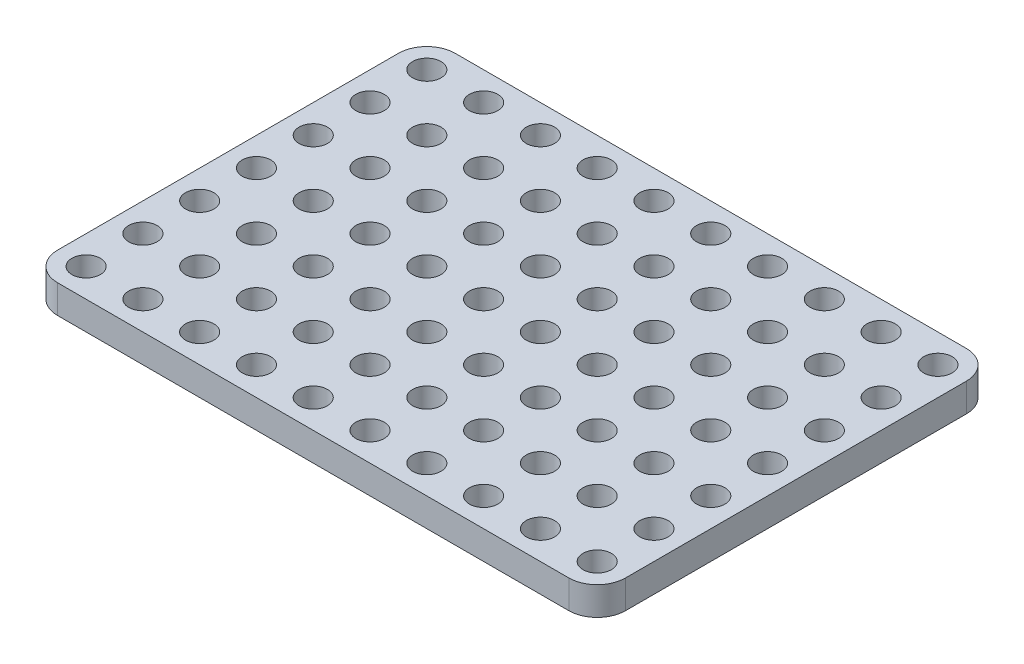
SolidWorks part; units mm, degrees
ref_plane "Front Plane" through (0, 0, 0) normal (0, 0, 1) x (1, 0, 0)
ref_plane "Top Plane" through (0, 0, 0) normal (0, 1, 0) x (1, 0, 0)
ref_plane "Right Plane" through (0, 0, 0) normal (1, 0, 0) x (0, 0, -1)
sketch "Sketch1" plane through (0, 0, 0) normal (0, 1, 0) x (1, 0, 0)
  line L1 (45, -35) -> (-45, -35)
  line L2 (50, -30) -> (50, 30)
  line L3 (45, 35) -> (-45, 35)
  line L4 (-50, -30) -> (-50, 30)
  line L5 (50, -35) -> (-50, 35) construction
  line L6 (50, 35) -> (-50, -35) construction
  arc A0 (45, 35) -> (50, 30) centre (45, 30) cw
  arc A1 (50, -30) -> (45, -35) centre (45, -30) cw
  arc A2 (-45, -35) -> (-50, -30) centre (-45, -30) cw
  arc A3 (-50, 30) -> (-45, 35) centre (-45, 30) cw
  circle A4 centre (-45, 30) radius 2.5
  circle A5 centre (-35, 30) radius 2.5
  circle A6 centre (-25, 30) radius 2.5
  circle A7 centre (-15, 30) radius 2.5
  circle A8 centre (-5, 30) radius 2.5
  circle A9 centre (5, 30) radius 2.5
  circle A10 centre (15, 30) radius 2.5
  circle A11 centre (25, 30) radius 2.5
  circle A12 centre (35, 30) radius 2.5
  circle A13 centre (45, 30) radius 2.5
  circle A14 centre (-35, 20) radius 2.5
  circle A15 centre (-25, 20) radius 2.5
  circle A16 centre (-15, 20) radius 2.5
  circle A17 centre (-5, 20) radius 2.5
  circle A18 centre (5, 20) radius 2.5
  circle A19 centre (15, 20) radius 2.5
  circle A20 centre (25, 20) radius 2.5
  circle A21 centre (35, 20) radius 2.5
  circle A22 centre (45, 20) radius 2.5
  circle A23 centre (-35, 10) radius 2.5
  circle A24 centre (-25, 10) radius 2.5
  circle A25 centre (-15, 10) radius 2.5
  circle A26 centre (-5, 10) radius 2.5
  circle A27 centre (5, 10) radius 2.5
  circle A28 centre (15, 10) radius 2.5
  circle A29 centre (25, 10) radius 2.5
  circle A30 centre (35, 10) radius 2.5
  circle A31 centre (45, 10) radius 2.5
  circle A32 centre (-35, 0) radius 2.5
  circle A33 centre (-25, 0) radius 2.5
  circle A34 centre (-15, 0) radius 2.5
  circle A35 centre (-5, 0) radius 2.5
  circle A36 centre (5, 0) radius 2.5
  circle A37 centre (15, 0) radius 2.5
  circle A38 centre (25, 0) radius 2.5
  circle A39 centre (35, 0) radius 2.5
  circle A40 centre (45, 0) radius 2.5
  circle A41 centre (-35, -10) radius 2.5
  circle A42 centre (-25, -10) radius 2.5
  circle A43 centre (-15, -10) radius 2.5
  circle A44 centre (-5, -10) radius 2.5
  circle A45 centre (5, -10) radius 2.5
  circle A46 centre (15, -10) radius 2.5
  circle A47 centre (25, -10) radius 2.5
  circle A48 centre (35, -10) radius 2.5
  circle A49 centre (45, -10) radius 2.5
  circle A50 centre (-35, -20) radius 2.5
  circle A51 centre (-25, -20) radius 2.5
  circle A52 centre (-15, -20) radius 2.5
  circle A53 centre (-5, -20) radius 2.5
  circle A54 centre (5, -20) radius 2.5
  circle A55 centre (15, -20) radius 2.5
  circle A56 centre (25, -20) radius 2.5
  circle A57 centre (35, -20) radius 2.5
  circle A58 centre (45, -20) radius 2.5
  circle A59 centre (-35, -30) radius 2.5
  circle A60 centre (-25, -30) radius 2.5
  circle A61 centre (-15, -30) radius 2.5
  circle A62 centre (-5, -30) radius 2.5
  circle A63 centre (5, -30) radius 2.5
  circle A64 centre (15, -30) radius 2.5
  circle A65 centre (25, -30) radius 2.5
  circle A66 centre (35, -30) radius 2.5
  circle A67 centre (45, -30) radius 2.5
  circle A68 centre (-45, 20) radius 2.5
  circle A69 centre (-45, 10) radius 2.5
  circle A70 centre (-45, 0) radius 2.5
  circle A71 centre (-45, -10) radius 2.5
  circle A72 centre (-45, -20) radius 2.5
  circle A73 centre (-45, -30) radius 2.5
  point P0 (0, 0)
  dimension "D3" = 5
  dimension "D4" = 5
  dimension "D1" = 100
  dimension "D2" = 70
  dimension "D5" = 7
extrude "Boss-Extrude1" add sketch "Sketch1" along normal blind 5
